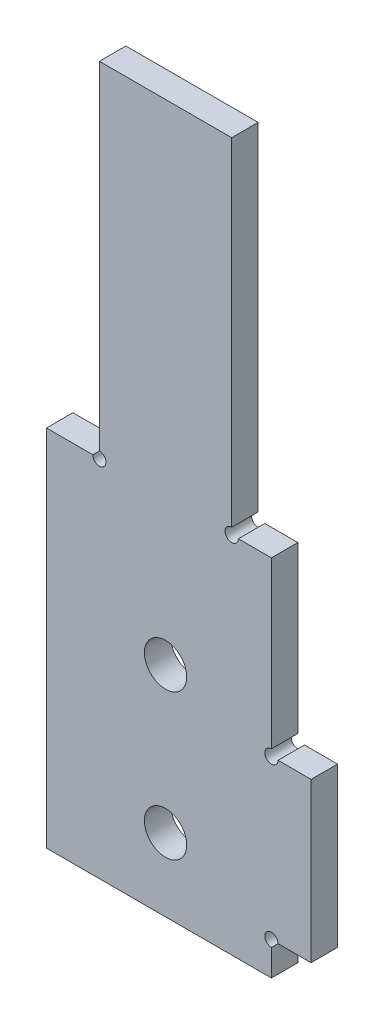
SolidWorks part; units mm, degrees
material "Thornel Mat VMA"
ref_plane "前视基准面" through (0, 0, 0) normal (0, 0, 1) x (1, 0, 0)
ref_plane "上视基准面" through (0, 0, 0) normal (0, 1, 0) x (1, 0, 0)
ref_plane "右视基准面" through (0, 0, 0) normal (1, 0, 0) x (0, 0, -1)
sketch "草图1" plane through (0, 0, 0) normal (0, 0, 1) x (1, 0, 0)
  line L1 (0, 0) -> (17, 0)
  line L2 (0, 0) -> (0, 51.5)
  line L3 (0, 51.5) -> (17, 51.5)
  line L4 (20, 2.5) -> (20, 14.5)
  line L7 (20, 2.5) -> (17, 2.5)
  line L8 (17, 0) -> (17, 2.5)
  line L11 (20, 14.5) -> (17, 14.5)
  line L12 (17, 51.5) -> (17, 14.5)
  point P11 (18.5, 2.5)
  dimension "D1" = 51.5
  dimension "D2" = 17
  dimension "D3" = 17
  dimension "D4" = 2.5
  dimension "D5" = 12
  dimension "D6" = 3
extrude "凸台-拉伸1" add sketch "草图1" along normal blind 2
sketch "草图2" plane through (0, 0, 2) normal (0, 0, 1) x (1, 0, 0)
  line L0 (0, 0) -> (17, 0) construction
  line L1 (0, 51.5) -> (0, 0) construction
  circle A0 centre (9, 5.5) radius 1.6
  circle A1 centre (9, 16.5) radius 1.6
  dimension "D1" = 3.2
  dimension "D2" = 3.2
  dimension "D3" = 5.5
  dimension "D4" = 9
  dimension "D5" = 11
  dimension "D6" = 9
extrude "切除-拉伸1" cut sketch "草图2" against normal through all
sketch "草图3" plane through (0, 0, 2) normal (0, 0, 1) x (1, 0, 0)
  line L0 (0, 0) -> (17, 0) construction
  line L1 (17, 51.5) -> (14, 51.5)
  line L2 (17, 51.5) -> (17, 27.5)
  line L3 (17, 27.5) -> (14, 27.5)
  line L4 (14, 51.5) -> (14, 27.5)
  line L6 (0, 51.5) -> (4, 51.5)
  line L7 (0, 51.5) -> (0, 27.5)
  line L8 (0, 27.5) -> (4, 27.5)
  line L9 (4, 51.5) -> (4, 27.5)
  dimension "D1" = 27.5
  dimension "D2" = 3
  dimension "D3" = 4
extrude "切除-拉伸2" cut sketch "草图3" against normal through all
sketch "草图4" plane through (0, 51.5, 0) normal (0, 1, 0) x (1, 0, 0)
  line L1 (4, -2) -> (14, -2)
  line L2 (4, -2) -> (4, 0)
  line L3 (4, 0) -> (14, 0)
  line L4 (14, -2) -> (14, 0)
extrude "凸台-拉伸2" add sketch "草图4" along normal blind 2
sketch "草图5" plane through (0, 0, 0) normal (0, 0, -1) x (-1, 0, 0)
  circle A0 centre (-14, 27.5) radius 0.5
  circle A1 centre (-4, 27.5) radius 0.5
  dimension "D1" = 1
  dimension "D2" = 1
extrude "切除-拉伸3" cut sketch "草图5" against normal blind 2
sketch "草图6" plane through (0, 0, 0) normal (0, 0, -1) x (-1, 0, 0)
  circle A0 centre (-17, 14.5) radius 0.5
  circle A1 centre (-17, 2.5) radius 0.5
  dimension "D1" = 1
  dimension "D2" = 1
extrude "切除-拉伸4" cut sketch "草图6" against normal blind 2
